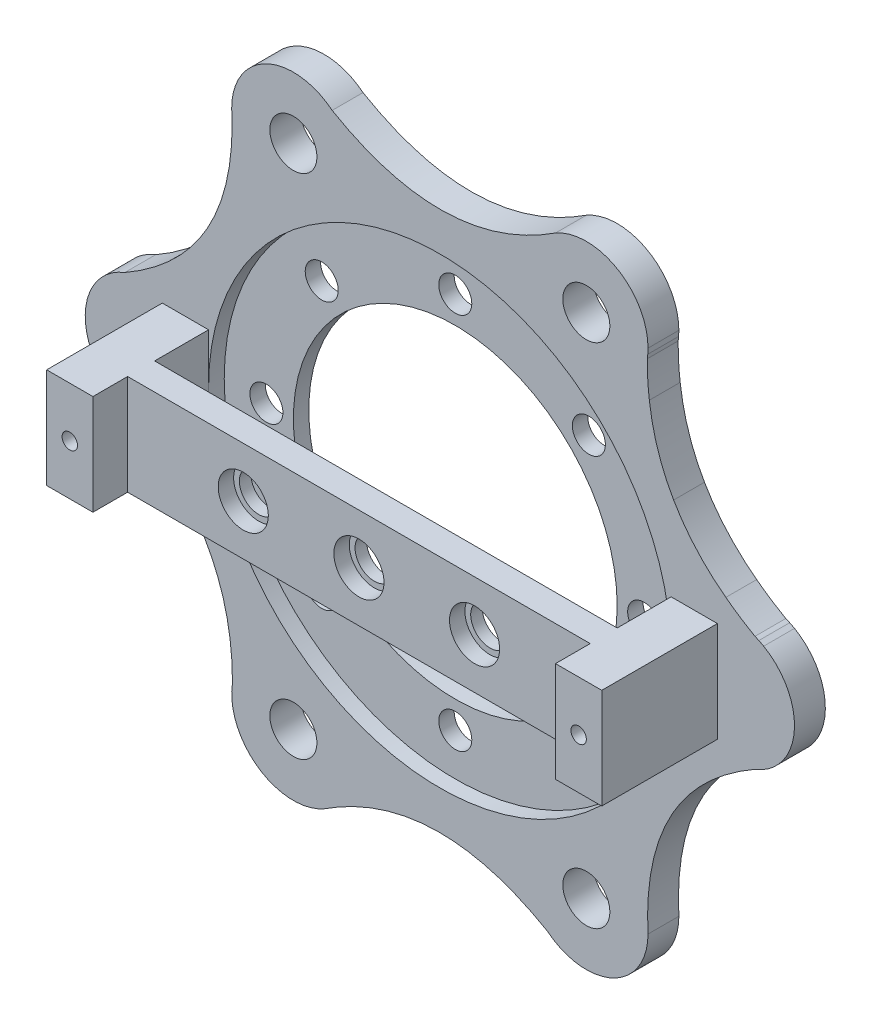
SolidWorks part; units mm, degrees
material "PVC 0.007 Plasticized"
ref_plane "Front Plane" through (0, 0, 0) normal (0, 0, 1) x (1, 0, 0)
ref_plane "Top Plane" through (0, 0, 0) normal (0, 1, 0) x (1, 0, 0)
ref_plane "Right Plane" through (0, 0, 0) normal (1, 0, 0) x (0, 0, -1)
sketch "Sketch1" plane through (0, 0, 0) normal (0, 0, 1) x (1, 0, 0)
  circle A0 centre (-37.0379, 0.1374) radius 3.05
  circle A1 centre (-18.0379, -32.7715) radius 3.05
  circle A2 centre (19.9621, -32.7715) radius 3.05
  circle A3 centre (38.9621, 0.1374) radius 3.05
  circle A4 centre (19.9621, 33.0464) radius 3.05
  circle A5 centre (-18.0379, 33.0464) radius 3.05
  circle A6 centre (0.9621, 0.1374) radius 30
  arc A8 (41.8311, -7.3304) -> (41.8311, 7.6053) centre (38.9621, 0.1374) ccw
  arc A9 (27.8639, 31.7971) -> (15.3684, 39.5961) centre (19.9621, 33.0464) ccw
  arc A10 (41.8311, -7.3304) -> (41.8311, 7.6053) centre (38.9621, 0.1374) ccw
  arc A11 (14.9292, -38.9901) -> (27.9311, -32.0681) centre (19.9621, -32.7715) ccw
  arc A12 (-25.9398, -31.5223) -> (-13.4443, -39.3212) centre (-18.0379, -32.7715) ccw
  arc A13 (-39.907, 7.6053) -> (-40.4133, -7.1156) centre (-37.0379, 0.1374) ccw
  arc A14 (-13.0051, 39.265) -> (-26.007, 32.343) centre (-18.0379, 33.0464) ccw
  spline S0 degree 2 poles (41.8311, 7.6053) (27.0544, 16.0568) (27.9621, 33.0464) knots 0 0 0 1 1 1
  spline S1 degree 2 poles (-25.9398, -31.5223) (-25.8707, -14.4995) (-41.0379, -6.7908) knots 0 0 0 1 1 1
  spline S2 degree 2 poles (-39.907, 7.6053) (-25.1303, 16.0568) (-26.0379, 33.0464) knots 0 0 0 1 1 1
  spline S3 degree 2 poles (-13.0051, 39.265) (1.7025, 30.6938) (15.9621, 39.9746) knots 0 0 0 1 1 1
  spline S4 degree 2 poles (27.8639, 31.7971) (27.7949, 14.7744) (42.9621, 7.0656) knots 0 0 0 1 1 1
  spline S5 degree 2 poles (41.8311, -7.3304) (27.0544, -15.782) (27.9621, -32.7715) knots 0 0 0 1 1 1
  spline S6 degree 2 poles (14.9292, -38.9901) (0.2216, -30.4189) (-14.0379, -39.6997) knots 0 0 0 1 1 1
  point P35 (0.9621, 0.1374)
  point P54 (0.9621, 0.1374)
  dimension "D2" = 6
extrude "Boss-Extrude1" add sketch "Sketch1" along normal blind 4 contours S6 A11 S5 A8 S4 S0 A9 S3 A14 S2 A13 S1 A12 A6 A5 A4 A3 A2 A1 A0 | A0 | A3
sketch "Sketch2" plane through (0, 0, 4) normal (0, 0, 1) x (1, 0, 0)
  line L4 (-29.0379, 0.1075) -> (30.9621, 0.1374) construction
  line L5 (0.9621, 0.1225) -> (0.9621, -42.9731) construction
  line L10 (-29.0379, 6.6075) -> (-29.0379, -6.3925)
  line L11 (-29.0379, 6.6075) -> (-35.0379, 6.6075)
  line L12 (-35.0379, 6.6075) -> (-35.0379, -6.3925)
  line L13 (-35.0379, -6.3925) -> (-29.0379, -6.3925)
  line L14 (36.9621, 6.6075) -> (36.9621, -6.3925)
  line L15 (30.9621, 6.6075) -> (36.9621, 6.6075)
  line L16 (30.9621, 6.6075) -> (30.9621, -6.3925)
  line L17 (36.9621, -6.3925) -> (30.9621, -6.3925)
  circle A0 centre (0.9621, 0.1374) radius 30 construction
  point P5 (-29.0379, 0.1075)
extrude "Boss-Extrude3" add sketch "Sketch2" along normal blind 15
sketch "Sketch3" plane through (30.9621, 0, 0) normal (-1, 0, 0) x (0, 0, 1)
  line L0 (4, 6.6075) -> (4, -6.3925) construction
  line L1 (4, -6.3925) -> (4, 0.1075) construction
  line L2 (4, 0.1075) -> (11, 0.1075) construction
  line L3 (19, 6.6075) -> (4, 6.6075) construction
  line L4 (11, 6.6075) -> (14.5, 6.6075)
  line L5 (11, 6.6075) -> (11, -6.3925)
  line L6 (11, -6.3925) -> (14.5, -6.3925)
  line L7 (14.5, 6.6075) -> (14.5, -6.3925)
  line L8 (19, -6.3925) -> (4, -6.3925) construction
extrude "Boss-Extrude4" add sketch "Sketch3" along normal up to surface (60 mm away) up to face at (-29.0379, 0.1135, 10)
sketch "Sketch4" plane through (0, 0, 14.5) normal (0, 0, 1) x (1, 0, 0)
  circle A3 centre (-14.0379, 0.1075) radius 2.5
  circle A4 centre (0.9621, 0.1075) radius 2.5
  circle A5 centre (15.9621, 0.1075) radius 2.5
  dimension "D1" = 3
extrude "Cut-Extrude2" cut sketch "Sketch4" against normal through all
sketch "Sketch5" plane through (0, 0, 14.5) normal (0, 0, 1) x (1, 0, 0)
  circle A1 centre (-14.0379, 0.1075) radius 3.25
  circle A2 centre (0.9621, 0.1075) radius 3.25
  circle A3 centre (15.9621, 0.1075) radius 3.25
extrude "Cut-Extrude3" cut sketch "Sketch5" against normal blind 2
sketch "Sketch6" plane through (0, 0, 4) normal (0, 0, 1) x (1, 0, 0)
  circle A0 centre (0.9621, 0.1075) radius 29.9701
  circle A1 centre (0.9621, 0.1075) radius 21
extrude "Boss-Extrude6" add sketch "Sketch6" against normal blind 2 from offset 2 separate body offset against normal yes
sketch "Sketch7" plane through (0, 0, 0) normal (0, 0, -1) x (-1, 0, 0)
  circle A0 centre (-0.9621, 0.1075) radius 24.5 construction
  circle A1 centre (-0.9621, 24.6075) radius 2.1412
  circle A2 centre (16.3621, 17.4316) radius 2.1412
  circle A3 centre (23.5379, 0.1075) radius 2.1412
  circle A4 centre (16.3621, -17.2166) radius 2.1412
  circle A5 centre (-0.9621, -24.3925) radius 2.1412
  circle A6 centre (-18.2862, -17.2166) radius 2.1412
  circle A7 centre (-25.4621, 0.1075) radius 2.1412
  circle A8 centre (-18.2862, 17.4316) radius 2.1412
  point P21 (-0.9621, 0.1075)
  dimension "D1" = 8
extrude "Cut-Extrude4" cut sketch "Sketch7" against normal up to surface (2 mm away) up to face at (21.9621, 0.1075, 2)
sketch "Sketch9" plane through (0, 0, 19) normal (0, 0, 1) x (1, 0, 0)
  line L2 (-35.0379, 6.6075) -> (-35.0379, -6.3925) construction
  line L3 (-29.0379, 6.6075) -> (-35.0379, 6.6075) construction
  line L5 (36.9621, 6.6075) -> (30.9621, 6.6075) construction
  circle A0 centre (33.9621, 0.1075) radius 1
  circle A1 centre (-32.0379, 0.1075) radius 1
  point P4 (0, 0)
  point P7 (-35.0379, 0.1075)
  point P10 (0, 0)
  point P11 (-32.0379, 6.6075)
  point P12 (0, 0)
  point P15 (0, 0)
  point P18 (33.9621, 6.6075)
  dimension "D1" = 2
extrude "Cut-Extrude5" cut sketch "Sketch9" against normal blind 9
